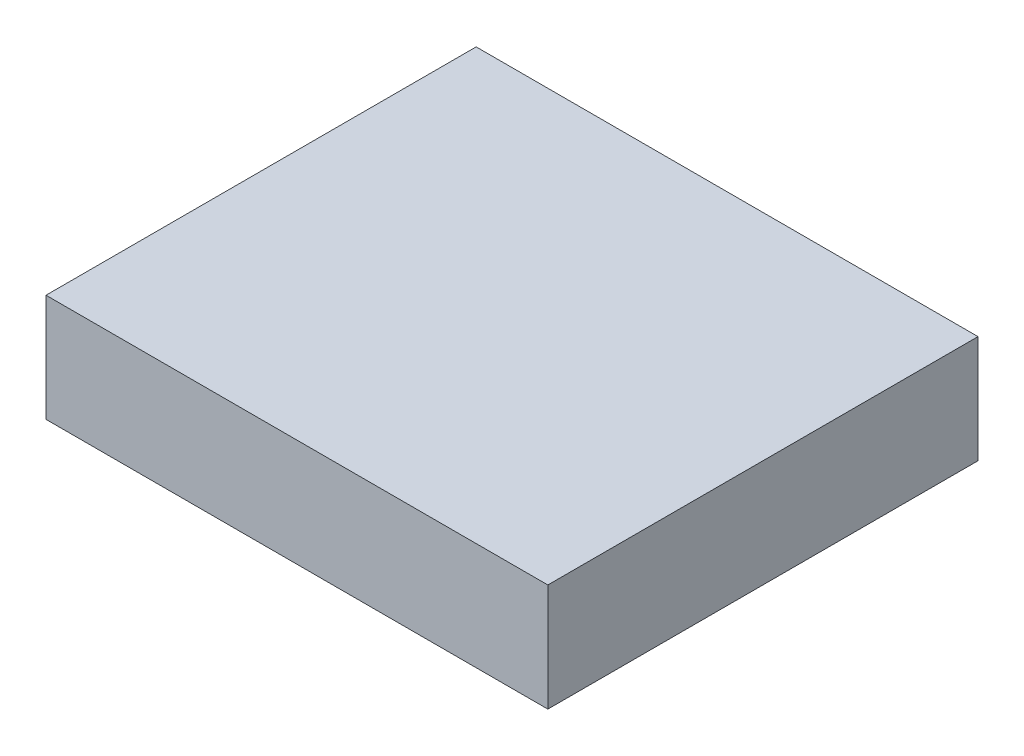
SolidWorks part; units mm, degrees
ref_plane "Front Plane" through (0, 0, 0) normal (0, 0, 1) x (1, 0, 0)
ref_plane "Top Plane" through (0, 0, 0) normal (0, 1, 0) x (1, 0, 0)
ref_plane "Right Plane" through (0, 0, 0) normal (1, 0, 0) x (0, 0, -1)
sketch "Sketch1" plane through (0, 0, 0) normal (0, 1, 0) x (1, 0, 0)
  line L1 (-1.8415, 0.8693) -> (1.6585, 0.8693)
  line L2 (-1.8415, 0.8693) -> (-1.8415, -2.1307)
  line L3 (-1.8415, -2.1307) -> (1.6585, -2.1307)
  line L4 (1.6585, 0.8693) -> (1.6585, -2.1307)
  dimension "D1" = 3.5
  dimension "D2" = 3
extrude "Boss-Extrude1" add sketch "Sketch1" along normal blind 0.75
